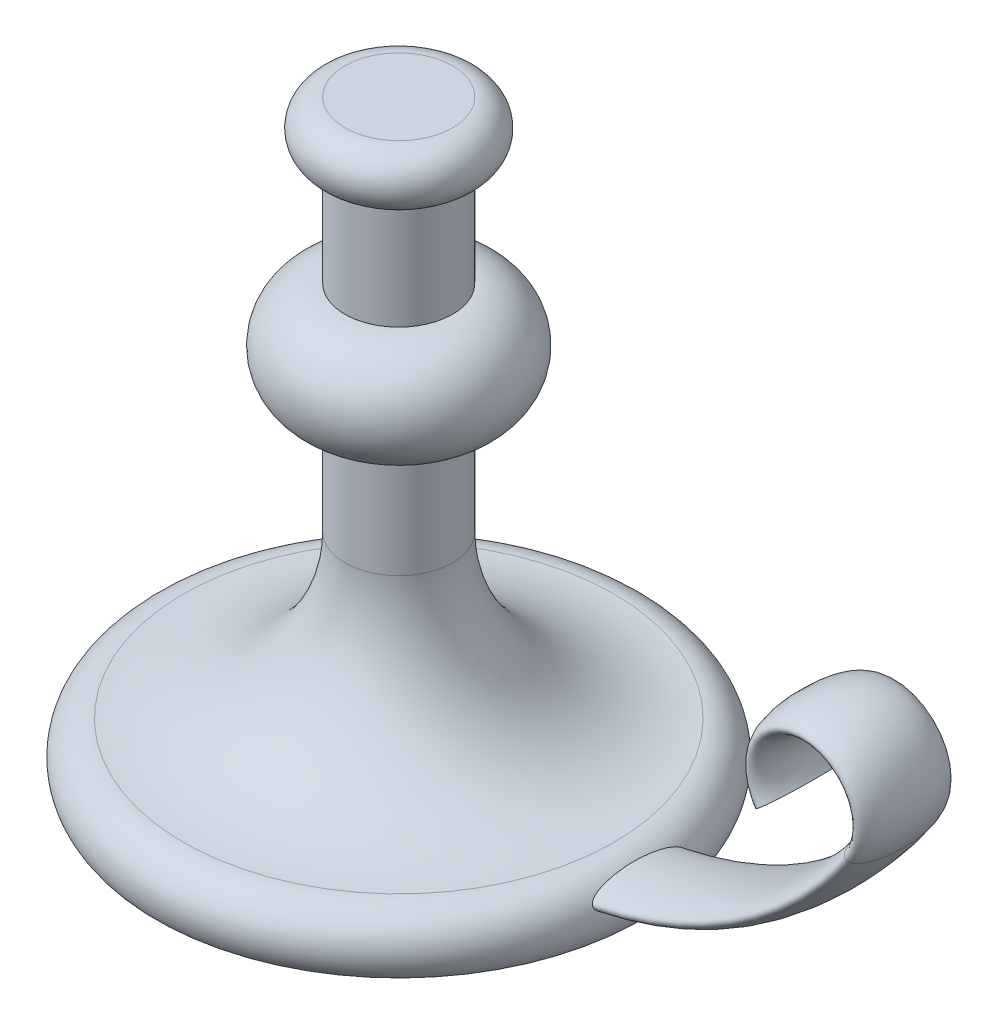
SolidWorks part; units mm, degrees
ref_plane "Alzado" through (0, 0, 0) normal (0, 0, 1) x (1, 0, 0)
ref_plane "Planta" through (0, 0, 0) normal (0, 1, 0) x (1, 0, 0)
ref_plane "Vista lateral" through (0, 0, 0) normal (1, 0, 0) x (0, 0, -1)
sketch "Croquis1" plane through (0, 0, 0) normal (0, 0, 1) x (1, 0, 0)
  line L0 (0, 0) -> (90, 0)
  line L1 (0, 0) -> (0, 220)
  line L2 (0, 220) -> (20, 220)
  line L3 (20, 200) -> (20, 160)
  line L4 (20, 120) -> (20, 80)
  arc A0 (20, 220) -> (20, 200) centre (20, 210) cw
  arc A1 (20, 160) -> (20, 120) centre (20, 140) cw
  arc A2 (20, 80) -> (80, 20) centre (80, 80) ccw
  arc A3 (80, 20) -> (90, 0) centre (80, 7.5) cw
  dimension "D4" = 10
  dimension "D5" = 20
  dimension "D7" = 60
  dimension "D8" = 12.5
  dimension "D1" = 90
  dimension "D2" = 220
  dimension "D3" = 20
  dimension "D6" = 40
  dimension "D9" = 80
revolve "Revolución1" add sketch "Croquis1" angle 360 about L1
sketch "Croquis2" plane through (0, 0, 0) normal (0, 0, 1) x (1, 0, 0)
  line L0 (0, 10) -> (60, 10)
  line L1 (0, 164) -> (0, 92) construction
  line L2 (0, 126.8188) -> (0, -13.6376) construction
  arc A0 (60, 10) -> (183.5921, 75) centre (60, 160) ccw
  arc A1 (183.5921, 75) -> (150.6342, 75) centre (167.1131, 86.3333) ccw
  dimension "D2" = 150
  dimension "D4" = 20
  dimension "D1" = 60
  dimension "D3" = 65
  dimension "D5" = 10
sketch "Croquis3" plane through (0, 0, 0) normal (1, 0, 0) x (0, 0, -1)
  line L0 (0, 75) -> (0, 10) construction
  ellipse E0 centre (0, 10) end of major axis (17.5, 10) minor radius 5
  dimension "D1" = 35
  dimension "D2" = 10
sweep "Barrer1" add profiles "Croquis3" path "Croquis2"
